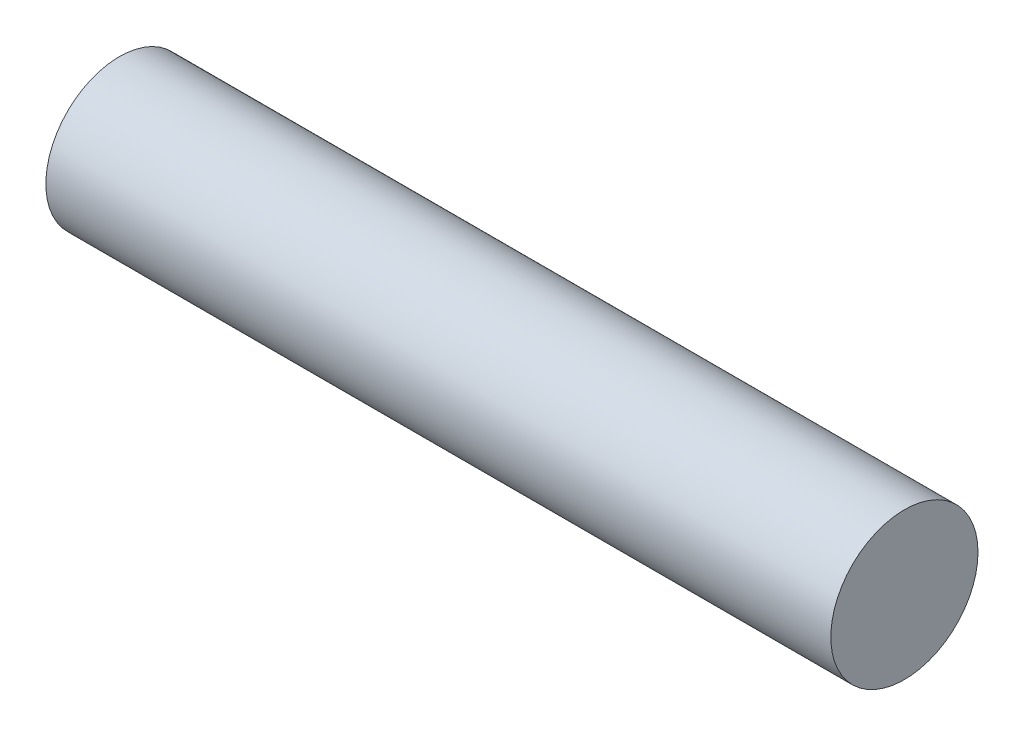
SolidWorks part; units mm, degrees
ref_plane "Front Plane" through (0, 0, 0) normal (0, 0, 1) x (1, 0, 0)
ref_plane "Top Plane" through (0, 0, 0) normal (0, 1, 0) x (1, 0, 0)
ref_plane "Right Plane" through (0, 0, 0) normal (1, 0, 0) x (0, 0, -1)
sketch "Sketch1" plane through (0, 0, 0) normal (1, 0, 0) x (0, 0, -1)
  circle A0 centre (0, 0) radius 1.5
  dimension "D1" = 3
extrude "Boss-Extrude1" add sketch "Sketch1" along normal blind 16
